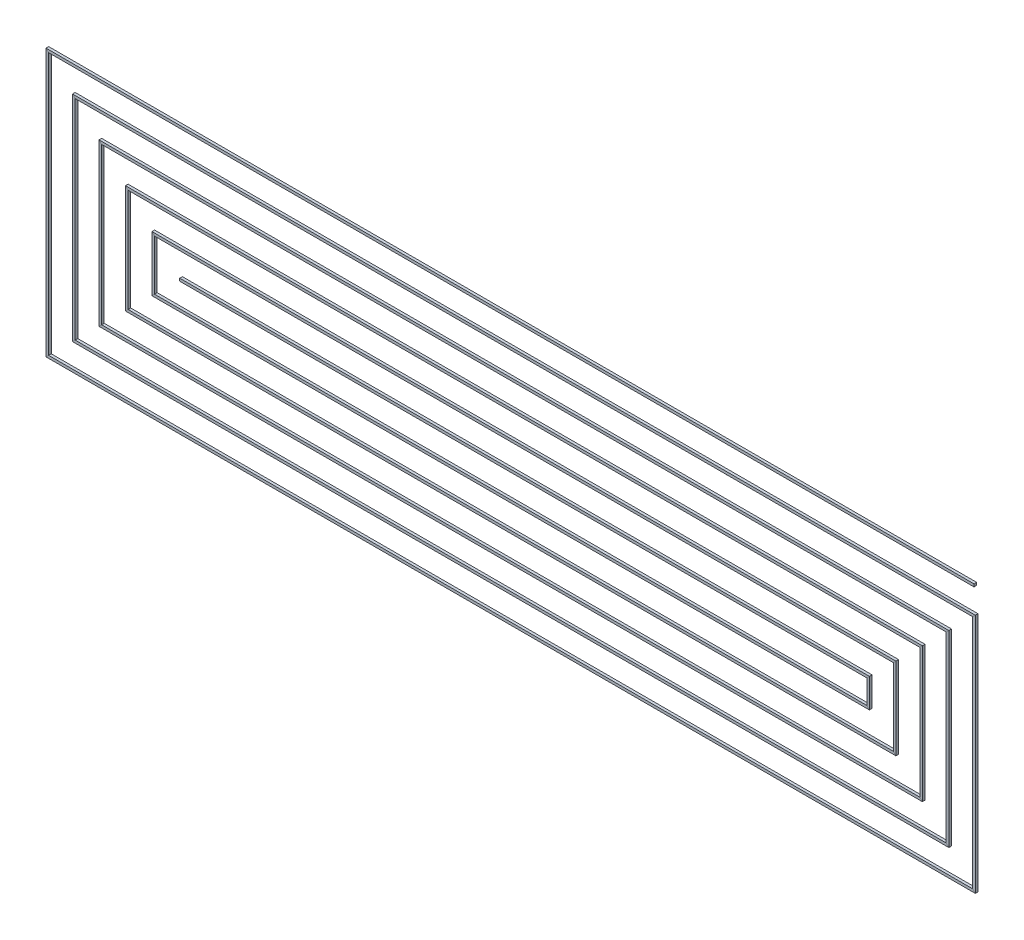
SolidWorks part; units mm, degrees
ref_plane "Front Plane" through (0, 0, 0) normal (0, 0, 1) x (1, 0, 0)
ref_plane "Top Plane" through (0, 0, 0) normal (0, 1, 0) x (1, 0, 0)
ref_plane "Right Plane" through (0, 0, 0) normal (1, 0, 0) x (0, 0, -1)
sketch "Sketch3" plane through (0, 0, 0) normal (0, 0, 1) x (1, 0, 0)
  line L0 (35, -10) -> (35, 8)
  line L1 (-35, -10) -> (35, -10)
  line L2 (-35, -10) -> (-35, 10)
  line L3 (-35, 10) -> (35, 10)
  line L5 (-35, -10) -> (35, 10) construction
  line L6 (-35, 10) -> (35, -10) construction
  line L7 (35, 8) -> (-33, 8)
  line L8 (-33, 8) -> (-33, -8)
  line L9 (-33, -8) -> (33, -8)
  line L10 (33, -8) -> (33, 6)
  line L11 (33, 6) -> (-31, 6)
  line L12 (-31, 6) -> (-31, -6)
  line L13 (-31, -6) -> (31, -6)
  line L14 (31, -6) -> (31, 4)
  line L15 (31, 4) -> (-29, 4)
  line L16 (-29, 4) -> (-29, -4)
  line L17 (-29, -4) -> (29, -4)
  line L18 (29, -4) -> (29, 2)
  line L19 (29, 2) -> (-27, 2)
  line L20 (-27, 2) -> (-27, -2)
  line L21 (-27, -2) -> (27, -2)
  line L22 (27, -2) -> (27, 0)
  line L23 (27, 0) -> (-25, 0)
  point P0 (0, 0)
  dimension "D1" = 20
  dimension "D2" = 70
  dimension "D3" = 18
  dimension "D4" = 68
  dimension "D5" = 16
  dimension "D6" = 66
  dimension "D7" = 14
  dimension "D8" = 64
  dimension "D9" = 12
  dimension "D10" = 62
  dimension "D11" = 10
  dimension "D12" = 60
  dimension "D13" = 8
  dimension "D14" = 58
  dimension "D15" = 6
  dimension "D16" = 56
  dimension "D17" = 4
  dimension "D18" = 54
  dimension "D19" = 2
  dimension "D20" = 52
sketch "Sketch4" plane through (0, 0, 0) normal (1, 0, 0) x (0, 0, -1)
  line L1 (-0.1, 0.1) -> (0.1, 0.1)
  line L2 (-0.1, 0.1) -> (-0.1, -0.1)
  line L3 (-0.1, -0.1) -> (0.1, -0.1)
  line L4 (0.1, 0.1) -> (0.1, -0.1)
  line L5 (-0.1, 0.1) -> (0.1, -0.1) construction
  line L6 (-0.1, -0.1) -> (0.1, 0.1) construction
  point P0 (0, 0)
  dimension "D1" = 0.2
sweep "Sweep2" add profiles "Sketch4" path "Sketch3"
